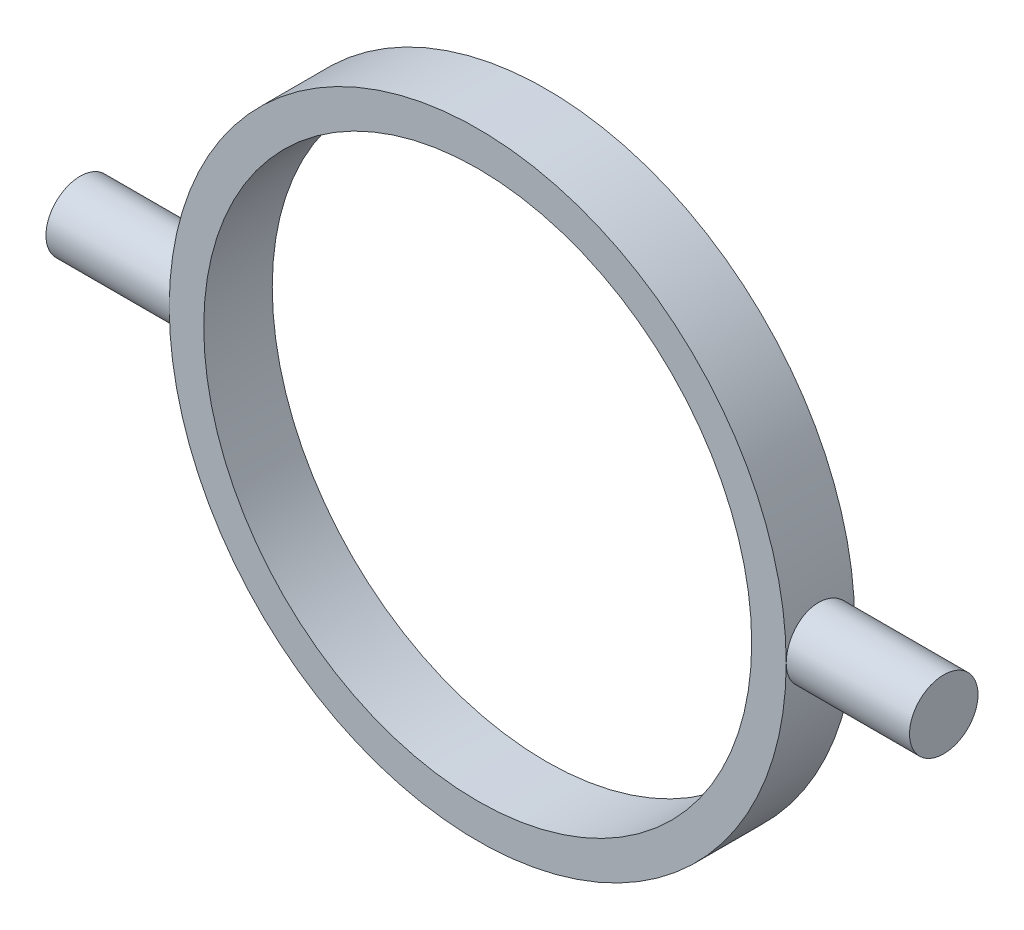
SolidWorks part; units mm, degrees
ref_plane "Front Plane" through (0, 0, 0) normal (0, 0, 1) x (1, 0, 0)
ref_plane "Top Plane" through (0, 0, 0) normal (0, 1, 0) x (1, 0, 0)
ref_plane "Right Plane" through (0, 0, 0) normal (1, 0, 0) x (0, 0, -1)
sketch "Sketch1" plane through (0, 0, 0) normal (0, 0, 1) x (1, 0, 0)
  circle A0 centre (0, 0) radius 12.7
  circle A1 centre (0, 0) radius 14.3
  dimension "D1" = 1.6
  dimension "D2" = 25.4
extrude "Boss-Extrude1" add sketch "Sketch1" along normal blind 3.175
ref_plane "Plane1" through (14.3, 0, 0) normal (1, 0, 0) x (0, 0, -1)
sketch "Sketch2" plane through (14.3, 0, 0) normal (1, 0, 0) x (0, 0, -1)
  line L0 (0, -14.3) -> (0, 14.3) construction
  line L4 (0, 0) -> (-1.5875, 0) construction
  circle A0 centre (-1.5875, 0) radius 1.5875
  dimension "D1" = 3.175
extrude "Boss-Extrude2" add sketch "Sketch2" along normal blind 5.715 and the other way blind 0.635
pattern_circular "CirPattern1" count 2 over 360 about axis through (0, 0, 3.175) along (0, 0, -1) of "Boss-Extrude2"
